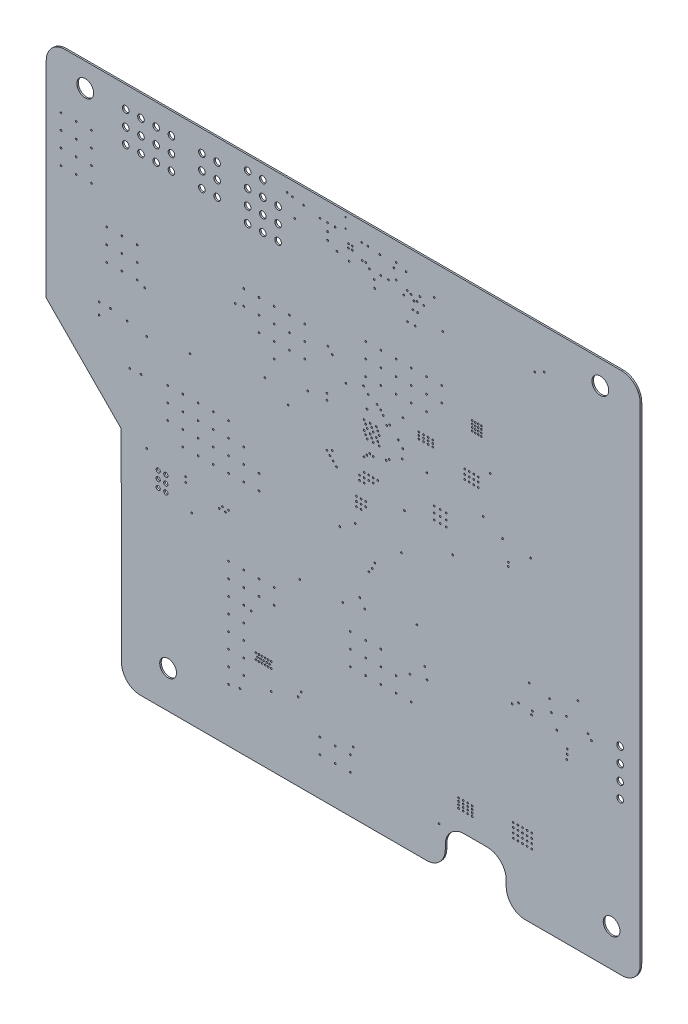
SolidWorks part; units mm, degrees
ref_plane "Front Plane" through (0, 0, 0) normal (0, 0, 1) x (1, 0, 0)
ref_plane "Top Plane" through (0, 0, 0) normal (0, 1, 0) x (1, 0, 0)
ref_plane "Right Plane" through (0, 0, 0) normal (1, 0, 0) x (0, 0, -1)
ref_plane "Conductive_Layer Bottom" through (0, 0, 0.034) normal (0, 0, 1) x (1, 0, 0)
ref_plane "Dielectric_Layer Bottom" through (0, 0, 0.288) normal (0, 0, 1) x (1, 0, 0)
ref_plane "Conductive_Layer Top" through (0, 0, 0.322) normal (0, 0, 1) x (1, 0, 0)
sketch "Sketch1" plane through (0, 0, 0) normal (0, 0, 1) x (1, 0, 0)
  line L0 (48.336, -41.631) -> (48.336, 39.37)
  line L1 (45.187, 42.52) -> (-47.549, 42.52)
  line L2 (-50.724, 39.37) -> (-50.724, 5.055)
  line L3 (-50.724, 5.055) -> (-38.227, -7.569)
  line L4 (-38.227, -7.569) -> (-38.176, -41.3)
  line L5 (-35.001, -44.475) -> (12.7, -44.475)
  line L6 (15.824, -41.275) -> (15.824, -40.615)
  line L7 (18.923, -37.49) -> (22.835, -37.49)
  line L8 (25.984, -40.615) -> (25.984, -41.631)
  line L9 (29.159, -44.806) -> (45.11, -44.806)
  arc A0 (45.11, -44.806) -> (48.336, -41.631) centre (45.2658, -41.7379) ccw
  arc A1 (48.336, 39.37) -> (45.187, 42.52) centre (45.2218, 39.4058) ccw
  arc A2 (-47.549, 42.52) -> (-50.724, 39.37) centre (-47.5697, 39.3658) ccw
  arc A3 (-38.176, -41.3) -> (-35.001, -44.475) centre (-35.0312, -41.3302) ccw
  arc A4 (12.7, -44.475) -> (15.824, -41.275) centre (12.6869, -41.3373) ccw
  arc A5 (15.824, -40.615) -> (18.923, -37.49) centre (18.9803, -40.6459) cw
  arc A6 (22.835, -37.49) -> (25.984, -40.615) centre (22.8195, -40.6547) cw
  arc A7 (25.984, -41.631) -> (29.159, -44.806) centre (29.1618, -41.6282) ccw
extrude "Board_Outline" add sketch "Sketch1" along normal blind 0.254 from offset 0.034 separate body
imported_body "Bottom"
imported_body "Top"
sketch "Sketch2" plane through (0, 0, 0) normal (0, 0, 1) x (1, 0, 0)
  circle A0 centre (-14.249, 11.76) radius 0.1395
  circle A1 centre (-10.388, 9.755) radius 0.1395
  circle A2 centre (-3.912, 13.691) radius 0.1395
  circle A3 centre (-2.311, 4.851) radius 0.1395
  circle A4 centre (-3.912, 14.681) radius 0.1395
  circle A5 centre (-3.912, 6.452) radius 0.1395
  circle A6 centre (-8.433, -14.478) radius 0.1395
  circle A7 centre (39.624, -12.7) radius 0.1395
  circle A8 centre (-7.806, 39.916) radius 0.1395
  circle A9 centre (-27.457, -9.957) radius 0.1395
  circle A10 centre (-27.483, -9.144) radius 0.1395
  circle A11 centre (-26.746, 8.992) radius 0.1395
  circle A12 centre (12.751, 11.532) radius 0.1395
  circle A13 centre (11.1, -11.252) radius 0.1395
  circle A14 centre (3.632, -6.858) radius 0.1395
  circle A15 centre (12.776, -18.364) radius 0.1395
  circle A16 centre (12.395, -16.612) radius 0.1395
  circle A17 centre (4.089, -5.817) radius 0.1395
  circle A18 centre (9.931, -18.974) radius 0.1395
  circle A19 centre (3.099, -7.595) radius 0.1395
  circle A20 centre (-1.753, -3.505) radius 0.1395
  circle A21 centre (-7.137, 13.411) radius 0.1395
  circle A22 centre (5.486, 16.18) radius 0.1395
  circle A23 centre (25.375, 8.357) radius 0.1395
  circle A24 centre (5.08, 16.764) radius 0.1395
  circle A25 centre (26.365, 5.41) radius 0.1395
  circle A26 centre (22.149, 9.931) radius 0.1395
  circle A27 centre (6.045, 15.011) radius 0.1395
  circle A28 centre (-3.023, 6.883) radius 0.1395
  circle A29 centre (-3.023, 20.701) radius 0.1395
  circle A30 centre (2.184, 18.796) radius 0.1395
  circle A31 centre (8.763, 17.475) radius 0.1395
  circle A32 centre (6.553, 15.367) radius 0.1395
  circle A33 centre (8.001, 13.919) radius 0.1395
  circle A34 centre (4.445, 17.247) radius 0.1395
  circle A35 centre (26.314, 4.775) radius 0.1395
  circle A36 centre (17.069, 1.854) radius 0.1395
  circle A37 centre (8.636, 11.481) radius 0.1395
  circle A38 centre (33.528, -12.7) radius 0.1395
  circle A39 centre (14.783, -38.125) radius 0.1395
  circle A40 centre (-33.964, -8.331) radius 0.1395
  circle A41 centre (-33.964, 7.844) radius 0.1395
  circle A42 centre (-19.177, 20.015) radius 0.1395
  circle A43 centre (-9.296, 37.236) radius 0.1395
  circle A44 centre (15.391, 33.271) radius 0.1395
  circle A45 centre (10.109, 35.972) radius 0.1395
  circle A46 centre (-26.441, -13.868) radius 0.1395
  circle A47 centre (2.972, 17.932) radius 0.1395
  circle A48 centre (23.317, 16.713) radius 0.1395
  circle A49 centre (2.769, 15.748) radius 0.1395
  circle A50 centre (0.813, -1.778) radius 0.1395
  circle A51 centre (30.048, 7.874) radius 0.1395
  circle A52 centre (8.738, 13.005) radius 0.1395
  circle A53 centre (-0.762, 17.704) radius 0.1395
  circle A54 centre (3.81, 9.398) radius 0.1395
  circle A55 centre (9.017, 4.216) radius 0.1395
  circle A56 centre (8.509, -2.134) radius 0.1395
  circle A57 centre (-0.808, 40.012) radius 0.1015
  circle A58 centre (-0.808, 41.686) radius 0.1015
  circle A59 centre (36.144, -17.424) radius 0.1395
  circle A60 centre (33.223, -10.846) radius 0.1395
  circle A61 centre (36.081, -18.199) radius 0.1395
  circle A62 centre (29.82, -10.287) radius 0.1395
  circle A63 centre (2.388, -13.326) radius 0.1395
  circle A64 centre (1.575, -12.09) radius 0.1395
  circle A65 centre (-36.779, 1.829) radius 0.1395
  circle A66 centre (-37.233, 8.455) radius 0.1395
  circle A67 centre (2.261, 8.585) radius 0.1395
  circle A68 centre (2.743, 9.068) radius 0.1395
  circle A69 centre (3.251, 9.55) radius 0.1395
  circle A70 centre (30.365, -14.06) radius 0.1395
  circle A71 centre (28.042, -14.06) radius 0.1395
  circle A72 centre (30.201, -14.707) radius 0.1395
  circle A73 centre (26.975, -14.707) radius 0.1395
  circle A74 centre (37.948, -8.788) radius 0.1395
  circle A75 centre (36.195, -16.637) radius 0.1395
  circle A76 centre (34.417, -14.808) radius 0.1395
  circle A77 centre (-8.179, -30.607) radius 0.1395
  circle A78 centre (-18.415, -35.204) radius 0.1395
  circle A79 centre (-1.27, -14.224) radius 0.1395
  circle A80 centre (-16.561, -23.063) radius 0.1395
  circle A81 centre (-8.712, -31.547) radius 0.1395
  circle A82 centre (0.457, -34.214) radius 0.1395
  circle A83 centre (-13.183, -33.02) radius 0.1395
  circle A84 centre (-34.315, 14.732) radius 0.1395
  circle A85 centre (-3.734, 21.565) radius 0.1395
  circle A86 centre (4.039, 33.833) radius 0.1395
  circle A87 centre (9.474, 36.246) radius 0.1395
  circle A88 centre (11.609, 36.424) radius 0.1395
  circle A89 centre (1.981, 36.818) radius 0.1395
  circle A90 centre (-0.212, 35.611) radius 0.1395
  circle A91 centre (-2.235, 36.017) radius 0.1395
  circle A92 centre (7.264, 38.379) radius 0.1395
  circle A93 centre (13.97, 37.465) radius 0.1395
  circle A94 centre (12.243, 35.458) radius 0.1395
  circle A95 centre (11.125, 35.458) radius 0.1395
  circle A96 centre (3.962, 35.077) radius 0.1395
  circle A97 centre (4.927, 39.129) radius 0.1395
  circle A98 centre (1.88, 39.345) radius 0.1395
  circle A99 centre (2.921, 39.345) radius 0.1395
  circle A100 centre (9.296, 38.862) radius 0.1395
  circle A101 centre (36.043, -11.989) radius 0.1395
  circle A102 centre (10.609, 35.281) radius 0.1395
  circle A103 centre (8.89, 35.281) radius 0.1395
  circle A104 centre (5.969, 9.957) radius 0.1395
  circle A105 centre (-10.542, 40.352) radius 0.1395
  circle A106 centre (32.317, 35.873) radius 0.1395
  circle A107 centre (30.74, 35.064) radius 0.1395
  circle A108 centre (6.502, 10.312) radius 0.1395
  circle A109 centre (-9.666, 40.178) radius 0.1395
extrude "Via" cut sketch "Sketch2" along normal through all
sketch "Sketch3" plane through (0, 0, 0) normal (0, 0, 1) x (1, 0, 0)
  circle A0 centre (41.681, 38.583) radius 1.397
  circle A1 centre (-44.221, 38.583) radius 1.397
  circle A2 centre (-30.404, -38.252) radius 1.397
  circle A3 centre (43.561, -38.557) radius 1.397
extrude "NPTH" cut sketch "Sketch3" along normal through all
sketch "Sketch4" plane through (0, 0, 0) normal (0, 0, 1) x (1, 0, 0)
  circle A0 centre (-22.225, 33.833) radius 0.55
  circle A1 centre (-24.765, 33.833) radius 0.55
  circle A2 centre (-22.225, 36.373) radius 0.55
  circle A3 centre (-24.765, 36.373) radius 0.55
  circle A4 centre (-22.225, 38.913) radius 0.55
  circle A5 centre (-24.765, 38.913) radius 0.55
  circle A6 centre (-14.605, 32.563) radius 0.55
  circle A7 centre (-17.145, 32.563) radius 0.55
  circle A8 centre (-14.605, 35.103) radius 0.55
  circle A9 centre (-17.145, 35.103) radius 0.55
  circle A10 centre (-14.605, 37.643) radius 0.55
  circle A11 centre (-17.145, 37.643) radius 0.55
  circle A12 centre (-14.605, 40.183) radius 0.55
  circle A13 centre (-17.145, 40.183) radius 0.55
  circle A14 centre (-29.845, 38.913) radius 0.55
  circle A15 centre (-32.385, 38.913) radius 0.55
  circle A16 centre (-34.925, 38.913) radius 0.55
  circle A17 centre (-37.465, 38.913) radius 0.55
  circle A18 centre (-29.845, 36.347) radius 0.55
  circle A19 centre (-32.385, 36.347) radius 0.55
  circle A20 centre (-34.925, 36.347) radius 0.55
  circle A21 centre (-37.465, 36.347) radius 0.55
  circle A22 centre (-29.845, 33.807) radius 0.55
  circle A23 centre (-32.385, 33.807) radius 0.55
  circle A24 centre (-34.925, 33.807) radius 0.55
  circle A25 centre (-37.465, 33.807) radius 0.55
  circle A26 centre (44.983, -19.456) radius 0.55
  circle A27 centre (44.983, -16.916) radius 0.55
  circle A28 centre (44.983, -14.376) radius 0.55
  circle A29 centre (44.983, -11.836) radius 0.55
  circle A30 centre (-30.785, -13.056) radius 0.35
  circle A31 centre (-30.785, -11.786) radius 0.35
  circle A32 centre (-30.785, -10.516) radius 0.35
  circle A33 centre (-32.055, -13.056) radius 0.35
  circle A34 centre (-32.055, -11.786) radius 0.35
  circle A35 centre (-32.055, -10.516) radius 0.35
  circle A36 centre (-12.065, 32.563) radius 0.55
  circle A37 centre (-12.065, 35.103) radius 0.55
  circle A38 centre (-12.065, 37.643) radius 0.55
  circle A39 centre (1.016, 2.286) radius 0.1395
  circle A40 centre (1.778, 2.286) radius 0.1395
  circle A41 centre (1.778, 1.524) radius 0.1395
  circle A42 centre (1.016, 1.524) radius 0.1395
  circle A43 centre (1.016, 0.762) radius 0.1395
  circle A44 centre (1.778, 0.762) radius 0.1395
  circle A45 centre (2.54, 2.286) radius 0.1395
  circle A46 centre (2.54, 1.524) radius 0.1395
  circle A47 centre (13.97, 7.366) radius 0.1395
  circle A48 centre (14.986, 7.366) radius 0.1395
  circle A49 centre (16.002, 7.366) radius 0.1395
  circle A50 centre (16.002, 6.35) radius 0.1395
  circle A51 centre (16.002, 5.334) radius 0.1395
  circle A52 centre (14.986, 6.35) radius 0.1395
  circle A53 centre (13.97, 6.35) radius 0.1395
  circle A54 centre (13.97, 5.334) radius 0.1395
  circle A55 centre (14.986, 5.334) radius 0.1395
  circle A56 centre (2.286, 13.97) radius 0.1395
  circle A57 centre (3.302, 13.97) radius 0.1395
  circle A58 centre (2.794, 12.954) radius 0.1395
  circle A59 centre (3.81, 12.954) radius 0.1395
  circle A60 centre (4.318, 13.97) radius 0.1395
  circle A61 centre (4.826, 12.954) radius 0.1395
  circle A62 centre (2.54, 13.462) radius 0.1395
  circle A63 centre (3.556, 13.462) radius 0.1395
  circle A64 centre (2.286, 12.446) radius 0.1395
  circle A65 centre (2.54, 11.938) radius 0.1395
  circle A66 centre (4.572, 13.462) radius 0.1395
  circle A67 centre (2.794, 11.43) radius 0.1395
  circle A68 centre (3.302, 12.446) radius 0.1395
  circle A69 centre (3.556, 11.938) radius 0.1395
  circle A70 centre (3.81, 11.43) radius 0.1395
  circle A71 centre (4.318, 12.446) radius 0.1395
  circle A72 centre (4.572, 11.938) radius 0.1395
  circle A73 centre (4.826, 11.43) radius 0.1395
  circle A74 centre (4.572, 6.35) radius 0.1395
  circle A75 centre (2.286, 6.35) radius 0.1395
  circle A76 centre (3.048, 6.35) radius 0.1395
  circle A77 centre (3.81, 6.35) radius 0.1395
  circle A78 centre (2.286, 5.588) radius 0.1395
  circle A79 centre (3.048, 5.588) radius 0.1395
  circle A80 centre (2.286, 4.826) radius 0.1395
  circle A81 centre (1.524, 5.588) radius 0.1395
  circle A82 centre (1.524, 4.826) radius 0.1395
  circle A83 centre (3.81, 5.588) radius 0.1395
  circle A84 centre (-15.748, -28.702) radius 0.1395
  circle A85 centre (-15.24, -28.702) radius 0.1395
  circle A86 centre (-14.732, -28.702) radius 0.1395
  circle A87 centre (-14.224, -28.702) radius 0.1395
  circle A88 centre (-13.716, -28.702) radius 0.1395
  circle A89 centre (-13.208, -28.702) radius 0.1395
  circle A90 centre (-15.494, -29.21) radius 0.1395
  circle A91 centre (-14.986, -29.21) radius 0.1395
  circle A92 centre (-14.478, -29.21) radius 0.1395
  circle A93 centre (-13.97, -29.21) radius 0.1395
  circle A94 centre (-13.462, -29.21) radius 0.1395
  circle A95 centre (-15.24, -29.718) radius 0.1395
  circle A96 centre (-14.732, -29.718) radius 0.1395
  circle A97 centre (-14.224, -29.718) radius 0.1395
  circle A98 centre (-13.716, -29.718) radius 0.1395
  circle A99 centre (-13.208, -29.718) radius 0.1395
  circle A100 centre (-15.748, -29.718) radius 0.1395
  circle A101 centre (-3.912, 14.681) radius 0.1395
  circle A102 centre (-2.87, 5.41) radius 0.1395
  circle A103 centre (-3.404, 5.944) radius 0.1395
  circle A104 centre (-30.48, 2.54) radius 0.1395
  circle A105 centre (20.32, 22.86) radius 0.1395
  circle A106 centre (20.32, 22.352) radius 0.1395
  circle A107 centre (20.32, 21.844) radius 0.1395
  circle A108 centre (20.32, 21.336) radius 0.1395
  circle A109 centre (20.828, 22.86) radius 0.1395
  circle A110 centre (20.828, 22.352) radius 0.1395
  circle A111 centre (20.828, 21.844) radius 0.1395
  circle A112 centre (20.828, 21.336) radius 0.1395
  circle A113 centre (21.336, 22.86) radius 0.1395
  circle A114 centre (21.336, 22.352) radius 0.1395
  circle A115 centre (21.336, 21.844) radius 0.1395
  circle A116 centre (21.336, 21.336) radius 0.1395
  circle A117 centre (21.844, 22.86) radius 0.1395
  circle A118 centre (21.844, 22.352) radius 0.1395
  circle A119 centre (21.844, 21.844) radius 0.1395
  circle A120 centre (21.844, 21.336) radius 0.1395
  circle A121 centre (18.034, -32.766) radius 0.1395
  circle A122 centre (18.796, -32.766) radius 0.1395
  circle A123 centre (19.558, -32.766) radius 0.1395
  circle A124 centre (20.32, -32.766) radius 0.1395
  circle A125 centre (20.32, -33.274) radius 0.1395
  circle A126 centre (19.558, -33.274) radius 0.1395
  circle A127 centre (18.796, -33.274) radius 0.1395
  circle A128 centre (18.034, -33.274) radius 0.1395
  circle A129 centre (18.034, -33.782) radius 0.1395
  circle A130 centre (18.796, -33.782) radius 0.1395
  circle A131 centre (19.558, -33.782) radius 0.1395
  circle A132 centre (20.32, -33.782) radius 0.1395
  circle A133 centre (20.32, -34.29) radius 0.1395
  circle A134 centre (19.558, -34.29) radius 0.1395
  circle A135 centre (18.796, -34.29) radius 0.1395
  circle A136 centre (18.034, -34.29) radius 0.1395
  circle A137 centre (27.178, -31.75) radius 0.1395
  circle A138 centre (27.94, -31.75) radius 0.1395
  circle A139 centre (28.702, -31.75) radius 0.1395
  circle A140 centre (29.464, -31.75) radius 0.1395
  circle A141 centre (30.226, -31.75) radius 0.1395
  circle A142 centre (29.464, -32.512) radius 0.1395
  circle A143 centre (30.226, -32.512) radius 0.1395
  circle A144 centre (28.702, -32.512) radius 0.1395
  circle A145 centre (27.94, -32.512) radius 0.1395
  circle A146 centre (27.178, -32.512) radius 0.1395
  circle A147 centre (27.178, -33.274) radius 0.1395
  circle A148 centre (27.94, -33.274) radius 0.1395
  circle A149 centre (28.702, -33.274) radius 0.1395
  circle A150 centre (29.464, -33.274) radius 0.1395
  circle A151 centre (30.226, -33.274) radius 0.1395
  circle A152 centre (30.226, -34.036) radius 0.1395
  circle A153 centre (29.464, -34.036) radius 0.1395
  circle A154 centre (28.702, -34.036) radius 0.1395
  circle A155 centre (27.94, -34.036) radius 0.1395
  circle A156 centre (27.178, -34.036) radius 0.1395
  circle A157 centre (11.43, 16.764) radius 0.1395
  circle A158 centre (12.192, 16.764) radius 0.1395
  circle A159 centre (12.954, 16.764) radius 0.1395
  circle A160 centre (13.716, 16.764) radius 0.1395
  circle A161 centre (11.43, 16.256) radius 0.1395
  circle A162 centre (12.192, 16.256) radius 0.1395
  circle A163 centre (12.954, 16.256) radius 0.1395
  circle A164 centre (13.716, 16.256) radius 0.1395
  circle A165 centre (13.716, 15.748) radius 0.1395
  circle A166 centre (12.954, 15.748) radius 0.1395
  circle A167 centre (12.192, 15.748) radius 0.1395
  circle A168 centre (11.43, 15.748) radius 0.1395
  circle A169 centre (-21.336, -10.414) radius 0.1395
  circle A170 centre (-20.32, -10.414) radius 0.1395
  circle A171 centre (-20.828, -10.922) radius 0.1395
  circle A172 centre (-21.844, -10.922) radius 0.1395
  circle A173 centre (-20.32, -17.78) radius 0.1395
  circle A174 centre (-17.78, -17.78) radius 0.1395
  circle A175 centre (-15.24, -17.78) radius 0.1395
  circle A176 centre (-12.7, -17.78) radius 0.1395
  circle A177 centre (-12.7, -20.32) radius 0.1395
  circle A178 centre (-15.24, -20.32) radius 0.1395
  circle A179 centre (-17.78, -20.32) radius 0.1395
  circle A180 centre (-20.32, -20.32) radius 0.1395
  circle A181 centre (-20.32, -22.86) radius 0.1395
  circle A182 centre (-17.78, -22.86) radius 0.1395
  circle A183 centre (-17.78, -25.4) radius 0.1395
  circle A184 centre (-20.32, -25.4) radius 0.1395
  circle A185 centre (-17.78, -27.94) radius 0.1395
  circle A186 centre (-20.32, -27.94) radius 0.1395
  circle A187 centre (-17.78, -30.48) radius 0.1395
  circle A188 centre (-20.32, -30.48) radius 0.1395
  circle A189 centre (-17.78, -33.02) radius 0.1395
  circle A190 centre (-20.32, -33.02) radius 0.1395
  circle A191 centre (-20.32, -35.56) radius 0.1395
  circle A192 centre (0, -17.78) radius 0.1395
  circle A193 centre (2.54, -17.78) radius 0.1395
  circle A194 centre (5.08, -17.78) radius 0.1395
  circle A195 centre (5.08, -20.32) radius 0.1395
  circle A196 centre (2.54, -20.32) radius 0.1395
  circle A197 centre (0, -20.32) radius 0.1395
  circle A198 centre (0, -22.86) radius 0.1395
  circle A199 centre (2.54, -22.86) radius 0.1395
  circle A200 centre (5.08, -22.86) radius 0.1395
  circle A201 centre (7.62, -22.86) radius 0.1395
  circle A202 centre (7.62, -20.32) radius 0.1395
  circle A203 centre (10.16, -22.86) radius 0.1395
  circle A204 centre (0, -38.1) radius 0.1395
  circle A205 centre (-2.54, -38.1) radius 0.1395
  circle A206 centre (-5.08, -38.1) radius 0.1395
  circle A207 centre (-5.08, -35.56) radius 0.1395
  circle A208 centre (-2.54, -35.56) radius 0.1395
  circle A209 centre (0, -35.56) radius 0.1395
  circle A210 centre (2.54, 20.32) radius 0.1395
  circle A211 centre (-15.24, 17.78) radius 0.1395
  circle A212 centre (19.05, 15.24) radius 0.1395
  circle A213 centre (19.05, 14.478) radius 0.1395
  circle A214 centre (19.05, 13.716) radius 0.1395
  circle A215 centre (19.812, 13.716) radius 0.1395
  circle A216 centre (19.812, 14.478) radius 0.1395
  circle A217 centre (19.812, 15.24) radius 0.1395
  circle A218 centre (20.574, 15.24) radius 0.1395
  circle A219 centre (20.574, 14.478) radius 0.1395
  circle A220 centre (20.574, 13.716) radius 0.1395
  circle A221 centre (21.336, 13.716) radius 0.1395
  circle A222 centre (21.336, 14.478) radius 0.1395
  circle A223 centre (21.336, 15.24) radius 0.1395
  circle A224 centre (5.08, 20.32) radius 0.1395
  circle A225 centre (7.62, 20.32) radius 0.1395
  circle A226 centre (10.16, 20.32) radius 0.1395
  circle A227 centre (12.7, 20.32) radius 0.1395
  circle A228 centre (2.54, 22.86) radius 0.1395
  circle A229 centre (5.08, 22.86) radius 0.1395
  circle A230 centre (7.62, 22.86) radius 0.1395
  circle A231 centre (10.16, 22.86) radius 0.1395
  circle A232 centre (12.7, 22.86) radius 0.1395
  circle A233 centre (2.54, 25.4) radius 0.1395
  circle A234 centre (5.08, 25.4) radius 0.1395
  circle A235 centre (7.62, 25.4) radius 0.1395
  circle A236 centre (10.16, 25.4) radius 0.1395
  circle A237 centre (12.7, 25.4) radius 0.1395
  circle A238 centre (15.24, 25.4) radius 0.1395
  circle A239 centre (15.24, 22.86) radius 0.1395
  circle A240 centre (-15.24, 20.32) radius 0.1395
  circle A241 centre (-17.78, 20.32) radius 0.1395
  circle A242 centre (-12.7, 17.78) radius 0.1395
  circle A243 centre (-12.7, 20.32) radius 0.1395
  circle A244 centre (-12.7, 15.24) radius 0.1395
  circle A245 centre (-10.16, 17.78) radius 0.1395
  circle A246 centre (-10.16, 20.32) radius 0.1395
  circle A247 centre (-7.62, 17.78) radius 0.1395
  circle A248 centre (-7.62, 20.32) radius 0.1395
  circle A249 centre (-17.78, 22.86) radius 0.1395
  circle A250 centre (-15.24, 22.86) radius 0.1395
  circle A251 centre (-12.7, 22.86) radius 0.1395
  circle A252 centre (-10.16, 22.86) radius 0.1395
  circle A253 centre (-7.62, 22.86) radius 0.1395
  circle A254 centre (-43.18, 25.4) radius 0.1395
  circle A255 centre (-45.72, 25.4) radius 0.1395
  circle A256 centre (-48.26, 25.4) radius 0.1395
  circle A257 centre (-48.26, 27.94) radius 0.1395
  circle A258 centre (-45.72, 27.94) radius 0.1395
  circle A259 centre (-43.18, 27.94) radius 0.1395
  circle A260 centre (-43.18, 30.48) radius 0.1395
  circle A261 centre (-45.72, 30.48) radius 0.1395
  circle A262 centre (-48.26, 30.48) radius 0.1395
  circle A263 centre (-48.26, 33.02) radius 0.1395
  circle A264 centre (-45.72, 33.02) radius 0.1395
  circle A265 centre (-43.18, 33.02) radius 0.1395
  circle A266 centre (-27.94, 2.54) radius 0.1395
  circle A267 centre (-25.4, 2.54) radius 0.1395
  circle A268 centre (-22.86, 2.54) radius 0.1395
  circle A269 centre (-20.32, 2.54) radius 0.1395
  circle A270 centre (-30.48, 0) radius 0.1395
  circle A271 centre (-27.94, 0) radius 0.1395
  circle A272 centre (-25.4, 0) radius 0.1395
  circle A273 centre (-22.86, 0) radius 0.1395
  circle A274 centre (-20.32, 0) radius 0.1395
  circle A275 centre (-17.78, 0) radius 0.1395
  circle A276 centre (-17.78, -2.54) radius 0.1395
  circle A277 centre (-20.32, -2.54) radius 0.1395
  circle A278 centre (-22.86, -2.54) radius 0.1395
  circle A279 centre (-25.4, -2.54) radius 0.1395
  circle A280 centre (-27.94, -2.54) radius 0.1395
  circle A281 centre (-30.48, -2.54) radius 0.1395
  circle A282 centre (-27.94, -5.08) radius 0.1395
  circle A283 centre (-25.4, -5.08) radius 0.1395
  circle A284 centre (-22.86, -5.08) radius 0.1395
  circle A285 centre (-20.32, -5.08) radius 0.1395
  circle A286 centre (-17.78, -5.08) radius 0.1395
  circle A287 centre (-15.24, -5.08) radius 0.1395
  circle A288 centre (-15.24, -2.54) radius 0.1395
  circle A289 centre (-40.64, 20.32) radius 0.1395
  circle A290 centre (-38.1, 20.32) radius 0.1395
  circle A291 centre (-35.56, 20.32) radius 0.1395
  circle A292 centre (-35.56, 17.78) radius 0.1395
  circle A293 centre (-38.1, 17.78) radius 0.1395
  circle A294 centre (-40.64, 17.78) radius 0.1395
  circle A295 centre (-40.64, 15.24) radius 0.1395
  circle A296 centre (-38.1, 15.24) radius 0.1395
  circle A297 centre (-35.56, 15.24) radius 0.1395
  circle A298 centre (-0.317, 38.1) radius 0.1395
  circle A299 centre (0.317, 38.1) radius 0.1395
  circle A300 centre (0.317, 37.465) radius 0.1395
  circle A301 centre (-0.317, 37.465) radius 0.1395
  circle A302 centre (10.439, 33.909) radius 0.1395
  circle A303 centre (11.201, 33.909) radius 0.1395
  circle A304 centre (10.795, 31.75) radius 0.1395
  circle A305 centre (9.525, 31.75) radius 0.1395
  circle A306 centre (-2.54, 39.37) radius 0.1395
  circle A307 centre (-3.81, 39.37) radius 0.1395
  circle A308 centre (-5.08, 39.37) radius 0.1395
  circle A309 centre (-3.81, 38.1) radius 0.1395
  circle A310 centre (-3.81, 36.83) radius 0.1395
  circle A311 centre (3.175, 36.195) radius 0.1395
  circle A312 centre (2.54, 36.83) radius 0.1395
  circle A313 centre (5.08, 36.195) radius 0.1395
  circle A314 centre (6.35, 36.195) radius 0.1395
  circle A315 centre (7.62, 36.83) radius 0.1395
  circle A316 centre (7.62, 39.37) radius 0.1395
  circle A317 centre (-34.925, 1.905) radius 0.1395
  circle A318 centre (-41.91, 6.985) radius 0.1395
  circle A319 centre (-41.91, 8.89) radius 0.1395
  circle A320 centre (-40.005, 8.89) radius 0.1395
  circle A321 centre (40.208, -13.411) radius 0.1395
extrude "PTH" cut sketch "Sketch4" along normal through all
ref_plane "z=0.322" through (0, 0, 0.322) normal (0, 0, 1) x (1, 0, 0)
sketch "Place_Keepout Shape6" plane through (0, 0, 0.322) normal (0, 0, 1) x (1, 0, 0)
  line L0 (3.48, -8.576) -> (5.357, -8.576)
  line L1 (5.357, -8.576) -> (5.357, -10.037)
  line L2 (5.357, -10.037) -> (3.48, -10.037)
  line L3 (3.48, -10.037) -> (3.48, -8.576)
ref_plane "Plane5" through (0, 0, 0.322) normal (0, 0, 1) x (1, 0, 0)
sketch "Place_Keepout Shape7" plane through (0, 0, 0.322) normal (0, 0, 1) x (1, 0, 0)
  line L0 (5.667, -8.576) -> (7.592, -8.576)
  line L1 (7.592, -8.576) -> (7.592, -10.027)
  line L2 (7.592, -10.027) -> (5.667, -10.027)
  line L3 (5.667, -10.027) -> (5.667, -8.576)
ref_plane "Plane6" through (0, 0, 0.322) normal (0, 0, 1) x (1, 0, 0)
sketch "Via_Keepout Shape6" plane through (0, 0, 0.322) normal (0, 0, 1) x (1, 0, 0)
  line L0 (3.48, -8.576) -> (5.357, -8.576)
  line L1 (5.357, -8.576) -> (5.357, -10.037)
  line L2 (5.357, -10.037) -> (3.48, -10.037)
  line L3 (3.48, -10.037) -> (3.48, -8.576)
ref_plane "Plane7" through (0, 0, 0.322) normal (0, 0, 1) x (1, 0, 0)
sketch "Via_Keepout Shape7" plane through (0, 0, 0.322) normal (0, 0, 1) x (1, 0, 0)
  line L0 (5.667, -8.576) -> (7.592, -8.576)
  line L1 (7.592, -8.576) -> (7.592, -10.027)
  line L2 (7.592, -10.027) -> (5.667, -10.027)
  line L3 (5.667, -10.027) -> (5.667, -8.576)
ref_plane "Plane8" through (0, 0, 0.322) normal (0, 0, 1) x (1, 0, 0)
sketch "Trace_Keepout Shape6" plane through (0, 0, 0.322) normal (0, 0, 1) x (1, 0, 0)
  line L0 (3.48, -8.576) -> (5.357, -8.576)
  line L1 (5.357, -8.576) -> (5.357, -10.037)
  line L2 (5.357, -10.037) -> (3.48, -10.037)
  line L3 (3.48, -10.037) -> (3.48, -8.576)
ref_plane "Plane9" through (0, 0, 0.322) normal (0, 0, 1) x (1, 0, 0)
sketch "Sketch10" plane through (0, 0, 0.322) normal (0, 0, 1) x (1, 0, 0)
  line L0 (3.48, -8.576) -> (5.357, -8.576)
  line L1 (5.357, -8.576) -> (5.357, -10.037)
  line L2 (5.357, -10.037) -> (3.48, -10.037)
  line L3 (3.48, -10.037) -> (3.48, -8.576)
ref_plane "Plane10" through (0, 0, 0.322) normal (0, 0, 1) x (1, 0, 0)
sketch "Trace_Keepout Shape7" plane through (0, 0, 0.322) normal (0, 0, 1) x (1, 0, 0)
  line L0 (5.667, -8.576) -> (7.592, -8.576)
  line L1 (7.592, -8.576) -> (7.592, -10.027)
  line L2 (7.592, -10.027) -> (5.667, -10.027)
  line L3 (5.667, -10.027) -> (5.667, -8.576)
ref_plane "Plane11" through (0, 0, 0.322) normal (0, 0, 1) x (1, 0, 0)
sketch "Sketch12" plane through (0, 0, 0.322) normal (0, 0, 1) x (1, 0, 0)
  line L0 (5.667, -8.576) -> (7.592, -8.576)
  line L1 (7.592, -8.576) -> (7.592, -10.027)
  line L2 (7.592, -10.027) -> (5.667, -10.027)
  line L3 (5.667, -10.027) -> (5.667, -8.576)
ref_plane "Plane12" through (0, 0, 0.322) normal (0, 0, 1) x (1, 0, 0)
sketch "Testpoint_Keepout Shape6" plane through (0, 0, 0.322) normal (0, 0, 1) x (1, 0, 0)
  line L0 (3.48, -8.576) -> (5.357, -8.576)
  line L1 (5.357, -8.576) -> (5.357, -10.037)
  line L2 (5.357, -10.037) -> (3.48, -10.037)
  line L3 (3.48, -10.037) -> (3.48, -8.576)
ref_plane "Plane13" through (0, 0, 0.322) normal (0, 0, 1) x (1, 0, 0)
sketch "Testpoint_Keepout Shape7" plane through (0, 0, 0.322) normal (0, 0, 1) x (1, 0, 0)
  line L0 (5.667, -8.576) -> (7.592, -8.576)
  line L1 (7.592, -8.576) -> (7.592, -10.027)
  line L2 (7.592, -10.027) -> (5.667, -10.027)
  line L3 (5.667, -10.027) -> (5.667, -8.576)
